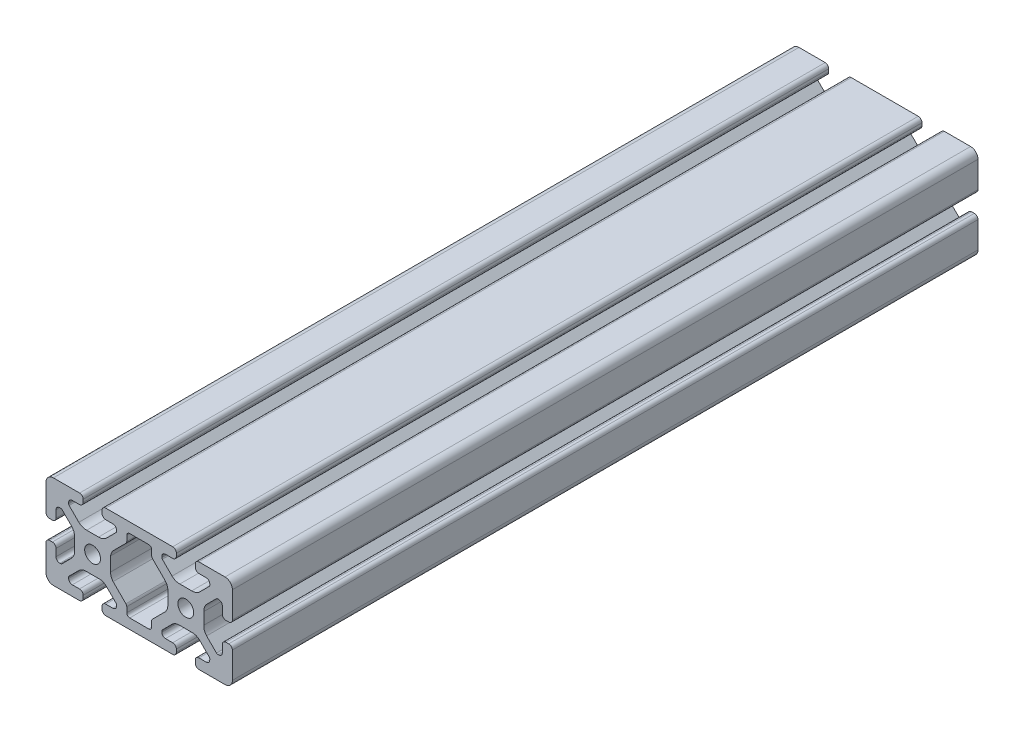
SolidWorks part; units mm, degrees
ref_plane "Front Plane" through (0, 0, 0) normal (0, 0, 1) x (1, 0, 0)
ref_plane "Top Plane" through (0, 0, 0) normal (0, 1, 0) x (1, 0, 0)
ref_plane "Right Plane" through (0, 0, 0) normal (1, 0, 0) x (0, 0, -1)
sketch "Sketch1" plane through (0, 0, 0) normal (0, 0, 1) x (1, 0, 0)
  line L0 (-14.3719, 20) -> (14.3719, 20)
  line L1 (-15.94, 17.1729) -> (-15.94, 18.3529)
  line L2 (-11.285, 15.68) -> (-14.37, 15.68)
  line L3 (-9.715, 13.6545) -> (-9.715, 14.11)
  line L4 (4.0718, 15.68) -> (-4.0718, 15.68)
  line L5 (-5.3418, 14.41) -> (-5.3418, 12.1296)
  line L6 (-5.7137, 11.2316) -> (-10.5988, 6.3465)
  line L7 (-12.2841, 3.2591) -> (-12.2841, -2.725)
  line L8 (5.991, -20) -> (-1.7801, -20)
  line L9 (0, 15.68) -> (0, -15.68) construction
  line L10 (-4.0718, -15.68) -> (4.0718, -15.68)
  line L11 (-5.3418, -12.1296) -> (-5.3418, -14.41)
  line L12 (-11.2012, -5.7441) -> (-5.7137, -11.2316)
  line L13 (-42.275, 0) -> (43.1806, 0) construction
  line L14 (-9.9376, 13.1171) -> (-14.0919, 8.9628)
  line L15 (-17.4506, 7.7) -> (-22.5494, 7.7)
  line L16 (-25.9081, 8.9628) -> (-30.0624, 13.1171)
  line L17 (-30.285, 13.6545) -> (-30.285, 14.11)
  line L18 (-28.715, 15.68) -> (-25.63, 15.68)
  line L19 (-24.06, 17.25) -> (-24.06, 18.4312)
  line L20 (-25.5696, 20) -> (-33, 20)
  line L21 (-33, 20) -> (-36.83, 20)
  line L22 (-40, 16.8406) -> (-40, 13.0106)
  line L23 (-40, 13.0106) -> (-40, 5.5825)
  line L24 (-38.3243, 4.06) -> (-37.1443, 4.06)
  line L25 (-35.68, 5.6264) -> (-35.68, 8.7114)
  line L26 (-34.11, 10.2814) -> (-33.6509, 10.2814)
  line L27 (-33.1135, 10.0588) -> (-29.0111, 5.9564)
  line L28 (-27.7159, 2.571) -> (-27.7159, -2.502)
  line L29 (-28.9155, -5.8608) -> (-33.1719, -10.1172)
  line L30 (-33.7093, -10.3398) -> (-34.111, -10.3398)
  line L31 (-35.68, -8.715) -> (-35.68, -5.63)
  line L32 (-37.25, -4.06) -> (-38.43, -4.06)
  line L33 (-40, -5.5696) -> (-40, -13)
  line L34 (-40, -13) -> (-40, -16.83)
  line L35 (-37.0574, -20) -> (-33.2274, -20)
  line L36 (-33.2274, -20) -> (-25.797, -20)
  line L37 (-24.06, -18.4389) -> (-24.06, -17.25)
  line L38 (-25.63, -15.68) -> (-28.715, -15.68)
  line L39 (-30.285, -14.11) -> (-30.285, -13.6545)
  line L40 (-30.0624, -13.1171) -> (-26.3095, -9.3642)
  line L41 (-23.3415, -7.7) -> (-16.6585, -7.7)
  line L42 (-13.6905, -9.3642) -> (-9.9376, -13.1171)
  line L43 (-9.715, -13.6545) -> (-9.715, -14.11)
  line L44 (-11.285, -15.68) -> (-14.37, -15.68)
  line L45 (-15.94, -17.25) -> (-15.94, -18.43)
  line L46 (-14.37, -20) -> (-5.991, -20)
  line L47 (-5.991, -20) -> (-1.7801, -20)
  line L48 (14.37, -20) -> (5.991, -20)
  line L49 (15.94, -17.25) -> (15.94, -18.43)
  line L50 (11.285, -15.68) -> (14.37, -15.68)
  line L51 (9.715, -13.6545) -> (9.715, -14.11)
  line L52 (13.6905, -9.3642) -> (9.9376, -13.1171)
  line L53 (23.3415, -7.7) -> (16.6585, -7.7)
  line L54 (30.0624, -13.1171) -> (26.3095, -9.3642)
  line L55 (30.285, -14.11) -> (30.285, -13.6545)
  line L56 (25.63, -15.68) -> (28.715, -15.68)
  line L57 (24.06, -18.4389) -> (24.06, -17.25)
  line L58 (33.2274, -20) -> (25.797, -20)
  line L59 (37.0574, -20) -> (33.2274, -20)
  line L60 (40, -13) -> (40, -16.83)
  line L61 (40, -5.5696) -> (40, -13)
  line L62 (37.25, -4.06) -> (38.4312, -4.06)
  line L63 (35.68, -8.715) -> (35.68, -5.63)
  line L64 (33.7093, -10.3398) -> (34.111, -10.3398)
  line L65 (28.9155, -5.8608) -> (33.1719, -10.1172)
  line L66 (27.7159, 2.571) -> (27.7159, -2.502)
  line L67 (33.1135, 10.0588) -> (29.0111, 5.9564)
  line L68 (34.11, 10.2814) -> (33.6509, 10.2814)
  line L69 (35.68, 5.6264) -> (35.68, 8.7114)
  line L70 (38.3243, 4.06) -> (37.1443, 4.06)
  line L71 (40, 13.0106) -> (40, 5.5825)
  line L72 (40, 16.8406) -> (40, 13.0106)
  line L73 (33, 20) -> (36.83, 20)
  line L74 (25.5696, 20) -> (33, 20)
  line L75 (24.06, 17.25) -> (24.06, 18.4312)
  line L76 (28.715, 15.68) -> (25.63, 15.68)
  line L77 (30.285, 13.6545) -> (30.285, 14.11)
  line L78 (25.9081, 8.9628) -> (30.0624, 13.1171)
  line L79 (17.4506, 7.7) -> (22.5494, 7.7)
  line L80 (9.9376, 13.1171) -> (14.0919, 8.9628)
  line L81 (11.2012, -5.7441) -> (5.7137, -11.2316)
  line L82 (5.3418, -12.1296) -> (5.3418, -14.41)
  line L83 (12.2841, 3.2591) -> (12.2841, -2.725)
  line L84 (5.7137, 11.2316) -> (10.5988, 6.3465)
  line L85 (5.3418, 14.41) -> (5.3418, 12.1296)
  line L86 (9.715, 13.6545) -> (9.715, 14.11)
  line L87 (11.285, 15.68) -> (14.37, 15.68)
  line L88 (15.94, 17.1729) -> (15.94, 18.3529)
  line L89 (-20, 24.8708) -> (-20, -18.43) construction
  line L90 (20, 29.4355) -> (20, -23.1087) construction
  line L91 (-3.0962, 16.9038) -> (-43.6857, -23.6857) construction
  line L92 (-36.2671, 16.2671) -> (-2.7875, -17.2125) construction
  arc A0 (-15.94, 18.3529) -> (-14.3719, 20) centre (-14.3719, 18.43) cw
  circle A1 centre (-20, 0) radius 3.4
  arc A2 (-14.37, 15.68) -> (-15.94, 17.1729) centre (-14.3719, 17.25) cw
  arc A3 (-11.285, 15.68) -> (-9.715, 14.11) centre (-11.285, 14.11) cw
  arc A4 (-9.715, 13.6545) -> (-9.9376, 13.1171) centre (-10.475, 13.6545) cw
  arc A5 (-12.2841, -2.725) -> (-11.2012, -5.7441) centre (-7.5341, -2.725) ccw
  arc A6 (-4.0718, 15.68) -> (-5.3418, 14.41) centre (-4.0718, 14.41) ccw
  arc A7 (-5.7137, 11.2316) -> (-5.3418, 12.1296) centre (-6.6118, 12.1296) ccw
  arc A8 (-10.5988, 6.3465) -> (-12.2841, 3.2591) centre (-7.5685, 2.6887) ccw
  arc A9 (-5.3418, -14.41) -> (-4.0718, -15.68) centre (-4.0718, -14.41) ccw
  arc A10 (-5.3418, -12.1296) -> (-5.7137, -11.2316) centre (-6.6118, -12.1296) ccw
  arc A11 (-17.4506, 7.7) -> (-14.0919, 8.9628) centre (-17.3191, 12.4482) ccw
  arc A12 (-25.9081, 8.9628) -> (-22.5494, 7.7) centre (-22.6809, 12.4482) ccw
  arc A13 (-30.285, 13.6545) -> (-30.0624, 13.1171) centre (-29.525, 13.6545) ccw
  arc A14 (-28.715, 15.68) -> (-30.285, 14.11) centre (-28.715, 14.11) ccw
  arc A15 (-25.63, 15.68) -> (-24.06, 17.25) centre (-25.63, 17.25) ccw
  arc A16 (-24.06, 18.4312) -> (-25.5696, 20) centre (-25.63, 18.4312) ccw
  arc A17 (-36.83, 20) -> (-40, 16.8406) centre (-36.83, 16.83) ccw
  arc A18 (-40, 5.5825) -> (-38.3243, 4.06) centre (-38.4306, 5.6264) ccw
  arc A19 (-37.1443, 4.06) -> (-35.68, 5.6264) centre (-37.25, 5.6264) ccw
  arc A20 (-34.11, 10.2814) -> (-35.68, 8.7114) centre (-34.11, 8.7114) ccw
  arc A21 (-33.1135, 10.0588) -> (-33.6509, 10.2814) centre (-33.6509, 9.5214) ccw
  arc A22 (-27.7159, 2.571) -> (-29.0111, 5.9564) centre (-32.4643, 2.6948) ccw
  arc A23 (-28.9155, -5.8608) -> (-27.7159, -2.502) centre (-32.4617, -2.7006) ccw
  arc A24 (-33.7093, -10.3398) -> (-33.1719, -10.1172) centre (-33.7093, -9.5798) ccw
  arc A25 (-35.68, -8.715) -> (-34.111, -10.3398) centre (-34.111, -8.7698) ccw
  arc A26 (-35.68, -5.63) -> (-37.25, -4.06) centre (-37.25, -5.63) ccw
  arc A27 (-38.43, -4.06) -> (-40, -5.5696) centre (-38.4312, -5.63) ccw
  arc A28 (-40, -16.83) -> (-37.0574, -20) centre (-36.83, -16.8382) ccw
  arc A29 (-25.797, -20) -> (-24.06, -18.4389) centre (-25.63, -18.4389) ccw
  arc A30 (-24.06, -17.25) -> (-25.63, -15.68) centre (-25.63, -17.25) ccw
  arc A31 (-30.285, -14.11) -> (-28.715, -15.68) centre (-28.715, -14.11) ccw
  arc A32 (-30.0624, -13.1171) -> (-30.285, -13.6545) centre (-29.525, -13.6545) ccw
  arc A33 (-23.3415, -7.7) -> (-26.3095, -9.3642) centre (-22.6565, -12.4003) ccw
  arc A34 (-13.6905, -9.3642) -> (-16.6585, -7.7) centre (-17.3435, -12.4003) ccw
  arc A35 (-9.715, -13.6545) -> (-9.9376, -13.1171) centre (-10.475, -13.6545) ccw
  arc A36 (-11.285, -15.68) -> (-9.715, -14.11) centre (-11.285, -14.11) ccw
  arc A37 (-14.37, -15.68) -> (-15.94, -17.25) centre (-14.37, -17.25) ccw
  arc A38 (-15.94, -18.43) -> (-14.37, -20) centre (-14.37, -18.43) ccw
  arc A39 (15.94, -18.43) -> (14.37, -20) centre (14.37, -18.43) cw
  arc A40 (14.37, -15.68) -> (15.94, -17.25) centre (14.37, -17.25) cw
  arc A41 (11.285, -15.68) -> (9.715, -14.11) centre (11.285, -14.11) cw
  arc A42 (9.715, -13.6545) -> (9.9376, -13.1171) centre (10.475, -13.6545) cw
  arc A43 (13.6905, -9.3642) -> (16.6585, -7.7) centre (17.3435, -12.4003) cw
  arc A44 (23.3415, -7.7) -> (26.3095, -9.3642) centre (22.6565, -12.4003) cw
  arc A45 (30.0624, -13.1171) -> (30.285, -13.6545) centre (29.525, -13.6545) cw
  arc A46 (30.285, -14.11) -> (28.715, -15.68) centre (28.715, -14.11) cw
  arc A47 (24.06, -17.25) -> (25.63, -15.68) centre (25.63, -17.25) cw
  arc A48 (25.797, -20) -> (24.06, -18.4389) centre (25.63, -18.4389) cw
  arc A49 (40, -16.83) -> (37.0574, -20) centre (36.83, -16.8382) cw
  arc A50 (38.4312, -4.06) -> (40, -5.5696) centre (38.4312, -5.63) cw
  arc A51 (35.68, -5.63) -> (37.25, -4.06) centre (37.25, -5.63) cw
  arc A52 (35.68, -8.715) -> (34.111, -10.3398) centre (34.111, -8.7698) cw
  arc A53 (33.7093, -10.3398) -> (33.1719, -10.1172) centre (33.7093, -9.5798) cw
  arc A54 (28.9155, -5.8608) -> (27.7159, -2.502) centre (32.4617, -2.7006) cw
  arc A55 (27.7159, 2.571) -> (29.0111, 5.9564) centre (32.4643, 2.6948) cw
  arc A56 (33.1135, 10.0588) -> (33.6509, 10.2814) centre (33.6509, 9.5214) cw
  arc A57 (34.11, 10.2814) -> (35.68, 8.7114) centre (34.11, 8.7114) cw
  arc A58 (37.1443, 4.06) -> (35.68, 5.6264) centre (37.25, 5.6264) cw
  arc A59 (40, 5.5825) -> (38.3243, 4.06) centre (38.4306, 5.6264) cw
  arc A60 (36.83, 20) -> (40, 16.8406) centre (36.83, 16.83) cw
  arc A61 (24.06, 18.4312) -> (25.5696, 20) centre (25.63, 18.4312) cw
  arc A62 (25.63, 15.68) -> (24.06, 17.25) centre (25.63, 17.25) cw
  arc A63 (28.715, 15.68) -> (30.285, 14.11) centre (28.715, 14.11) cw
  arc A64 (30.285, 13.6545) -> (30.0624, 13.1171) centre (29.525, 13.6545) cw
  arc A65 (25.9081, 8.9628) -> (22.5494, 7.7) centre (22.6809, 12.4482) cw
  arc A66 (17.4506, 7.7) -> (14.0919, 8.9628) centre (17.3191, 12.4482) cw
  arc A67 (5.3418, -12.1296) -> (5.7137, -11.2316) centre (6.6118, -12.1296) cw
  arc A68 (5.3418, -14.41) -> (4.0718, -15.68) centre (4.0718, -14.41) cw
  arc A69 (10.5988, 6.3465) -> (12.2841, 3.2591) centre (7.5685, 2.6887) cw
  arc A70 (5.7137, 11.2316) -> (5.3418, 12.1296) centre (6.6118, 12.1296) cw
  arc A71 (4.0718, 15.68) -> (5.3418, 14.41) centre (4.0718, 14.41) cw
  arc A72 (12.2841, -2.725) -> (11.2012, -5.7441) centre (7.5341, -2.725) cw
  arc A73 (9.715, 13.6545) -> (9.9376, 13.1171) centre (10.475, 13.6545) ccw
  arc A74 (11.285, 15.68) -> (9.715, 14.11) centre (11.285, 14.11) ccw
  arc A75 (14.37, 15.68) -> (15.94, 17.1729) centre (14.3719, 17.25) ccw
  circle A76 centre (20, 0) radius 3.4
  arc A77 (15.94, 18.3529) -> (14.3719, 20) centre (14.3719, 18.43) ccw
  dimension "D4" = 6.8
  dimension "D1" = 80
  dimension "D2" = 40
  dimension "D3" = 20
  dimension "D5" = 8.12
  dimension "D6" = 4.32
  dimension "D7" = 20.57
  dimension "D8" = 4.32
  dimension "D9" = 12.3
  dimension "D10" = 8.12
  dimension "D11" = 4.32
  dimension "D12" = 4.32
  dimension "D13" = 4.32
extrude "Boss-Extrude1" add sketch "Sketch1" along normal blind 320
